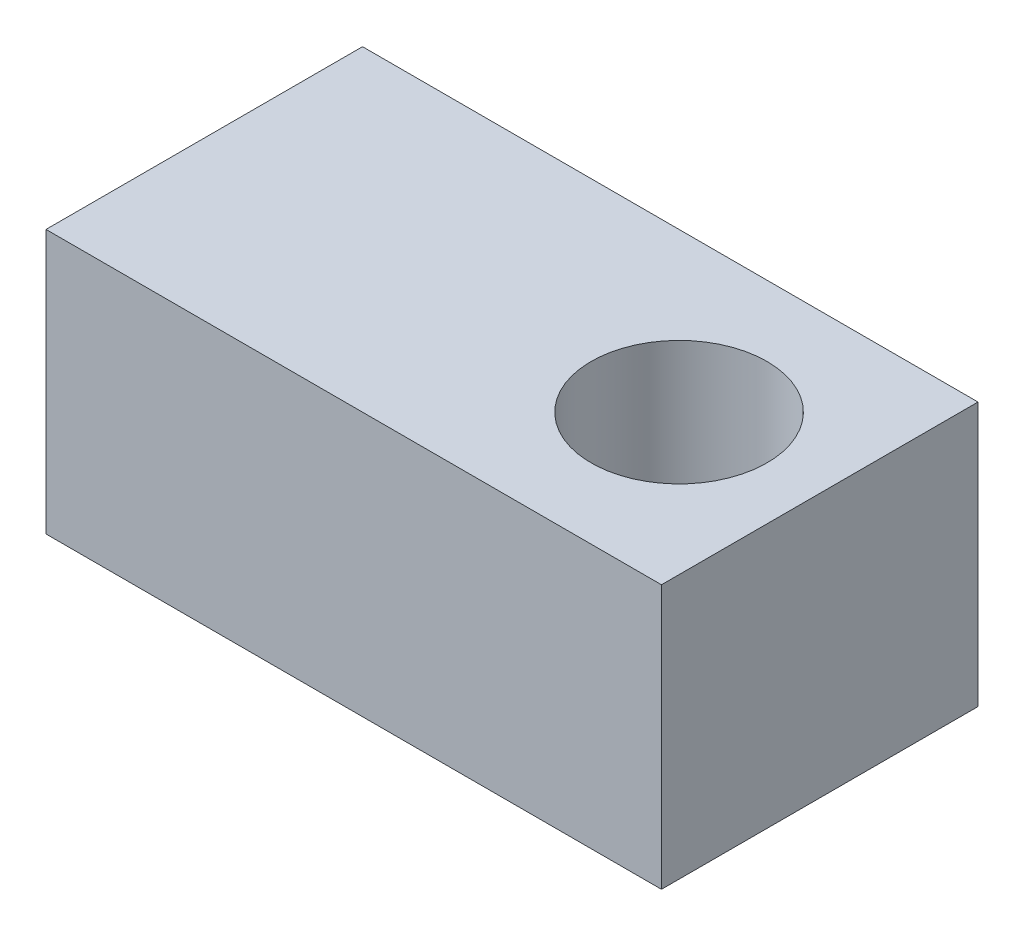
SolidWorks part; units mm, degrees
ref_plane "Front Plane" through (0, 0, 0) normal (0, 0, 1) x (1, 0, 0)
ref_plane "Top Plane" through (0, 0, 0) normal (0, 1, 0) x (1, 0, 0)
ref_plane "Right Plane" through (0, 0, 0) normal (1, 0, 0) x (0, 0, -1)
sketch "Sketch1" plane through (0, 0, 0) normal (1, 0, 0) x (0, 0, -1)
  line L1 (-27.7826, 12.913) -> (-9.7826, 12.913)
  line L2 (-27.7826, 12.913) -> (-27.7826, -2.087)
  line L3 (-27.7826, -2.087) -> (-9.7826, -2.087)
  line L4 (-9.7826, 12.913) -> (-9.7826, -2.087)
  dimension "D1" = 18
  dimension "D2" = 15
extrude "Boss-Extrude1" add sketch "Sketch1" along normal blind 35
sketch "Sketch2" plane through (0, -2.087, 0) normal (0, -1, 0) x (-1, 0, 0)
  line L0 (0, -27.7826) -> (0, -9.7826) construction
  line L1 (-35, -27.7826) -> (0, -27.7826) construction
  circle A0 centre (-27, -18.7826) radius 5
  dimension "D1" = 10
  dimension "D2" = 27
  dimension "D3" = 9
extrude "Cut-Extrude1" cut sketch "Sketch2" against normal through all contours A0
sketch "Sketch3" plane through (0, 0, 0) normal (-1, 0, 0) x (0, 0, 1)
  circle A0 centre (18.7826, 5.413) radius 3
  dimension "D1" = 6
extrude "Cut-Extrude2" cut sketch "Sketch3" against normal blind 8
